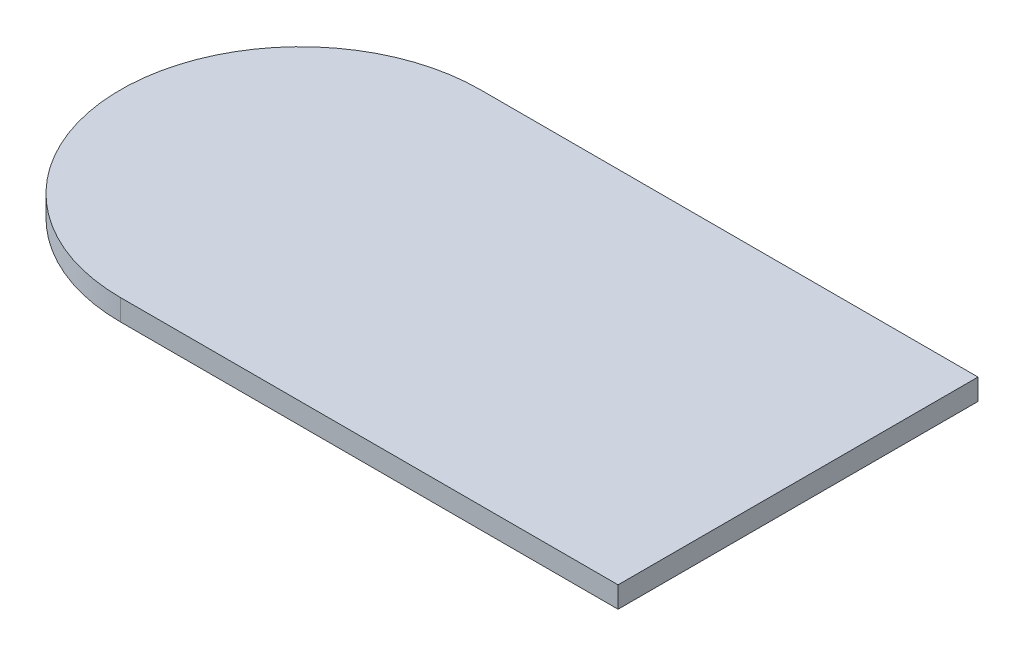
SolidWorks part; units mm, degrees
ref_plane "Front Plane" through (0, 0, 0) normal (0, 0, 1) x (1, 0, 0)
ref_plane "Top Plane" through (0, 0, 0) normal (0, 1, 0) x (1, 0, 0)
ref_plane "Right Plane" through (0, 0, 0) normal (1, 0, 0) x (0, 0, -1)
sketch "Sketch2" plane through (0, 0, 0) normal (0, 1, 0) x (1, 0, 0)
  line L0 (0, 21.59) -> (59.6958, 21.59)
  line L1 (59.6958, 21.59) -> (59.6958, -21.59)
  line L2 (59.6958, -21.59) -> (0, -21.59)
  arc A0 (0, 21.59) -> (0, -21.59) centre (0, 0) ccw
  dimension "D1" = 43.18
extrude "Boss-Extrude1" add sketch "Sketch2" along normal blind 2.54
